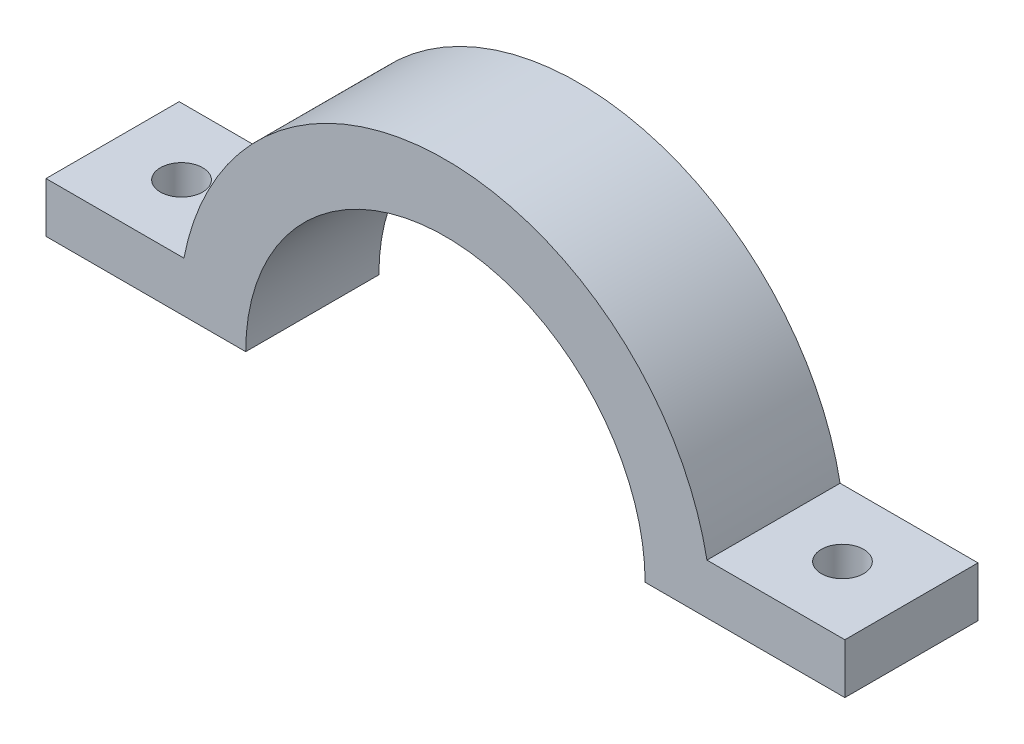
SolidWorks part; units mm, degrees
ref_plane "Front Plane" through (0, 0, 0) normal (0, 0, 1) x (1, 0, 0)
ref_plane "Top Plane" through (0, 0, 0) normal (0, 1, 0) x (1, 0, 0)
ref_plane "Right Plane" through (0, 0, 0) normal (1, 0, 0) x (0, 0, -1)
sketch "Sketch1" plane through (0, 0, 0) normal (0, 0, 1) x (1, 0, 0)
  line L0 (-20, 0) -> (-15, 0)
  line L1 (15, 0) -> (20, 0)
  line L2 (20, 0) -> (30, 0)
  line L3 (30, 0) -> (30, 3.7657)
  line L4 (30, 3.7657) -> (19.6423, 3.7657)
  line L5 (0, 0) -> (0, 20) construction
  line L6 (-30, 3.7657) -> (-19.6423, 3.7657)
  line L7 (-30, 0) -> (-30, 3.7657)
  line L8 (-20, 0) -> (-30, 0)
  arc A0 (-15, 0) -> (15, 0) centre (0, 0) cw
  arc A1 (-20, 0) -> (20, 0) centre (0, 0) cw construction
  arc A2 (-19.6423, 3.7657) -> (19.6423, 3.7657) centre (0, 0) cw
  dimension "D1" = 15
  dimension "D2" = 5
  dimension "D3" = 10
extrude "Boss-Extrude1" add sketch "Sketch1" along normal blind 10
ref_plane "Plane1" through (0, 0, 0) normal (-1, 0, 0) x (0, 0, 1)
sketch "Sketch2" plane through (0, 3.7657, 0) normal (0, 1, 0) x (1, 0, 0)
  circle A0 centre (24.8211, -5) radius 1.5875
  dimension "D1" = 3.175
extrude "Cut-Extrude1" cut sketch "Sketch2" against normal up to surface (3.7657 mm away) up to face at (22.5, 0, 5)
mirror "Mirror1" about plane through (0, 0, 0) normal (-1, 0, 0) of "Cut-Extrude1"
